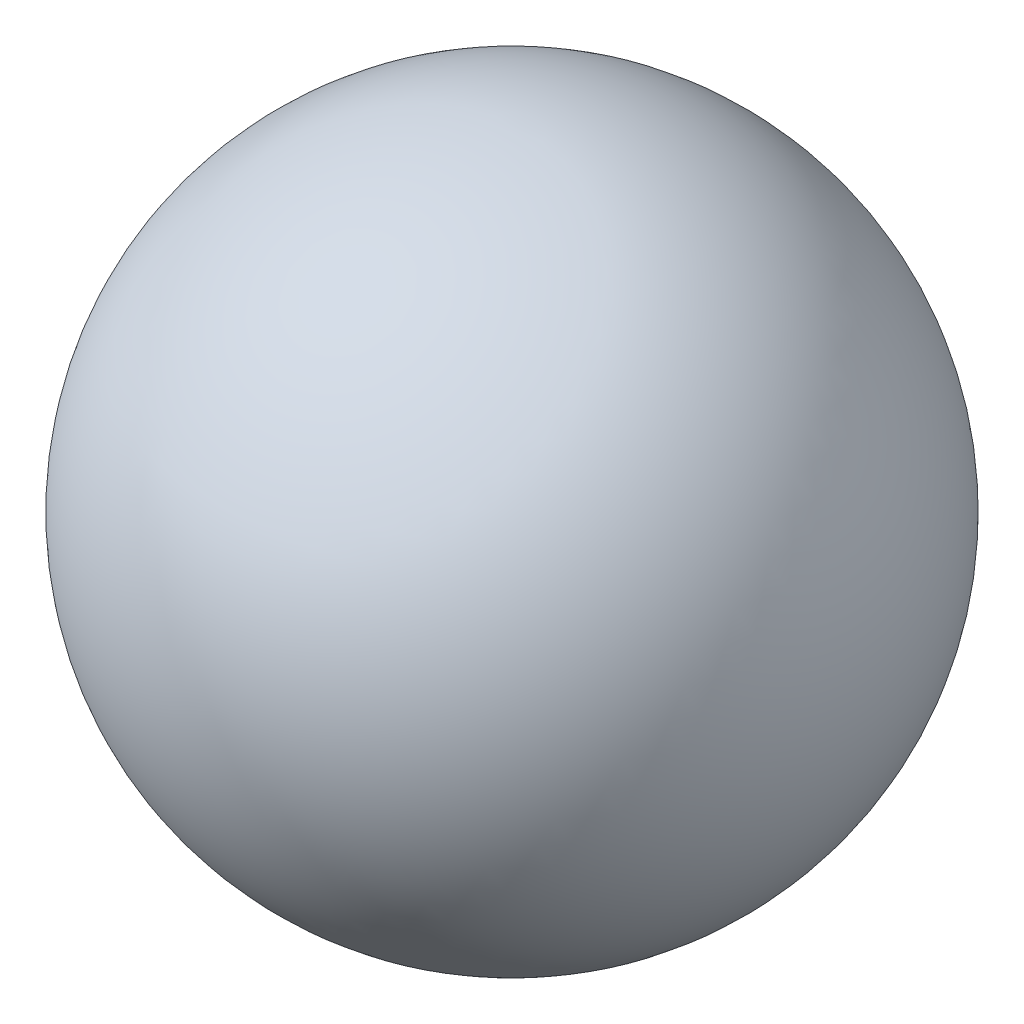
SolidWorks part; units mm, degrees
ref_plane "Front Plane" through (0, 0, 0) normal (0, 0, 1) x (1, 0, 0)
ref_plane "Top Plane" through (0, 0, 0) normal (0, 1, 0) x (1, 0, 0)
ref_plane "Right Plane" through (0, 0, 0) normal (1, 0, 0) x (0, 0, -1)
sketch "Sketch1" plane through (0, 0, 0) normal (1, 0, 0) x (0, 0, -1)
  line L0 (0, 0) -> (0, -21.5) construction
  line L1 (0, 21.5) -> (0, -21.5)
  arc A0 (0, -21.5) -> (0, 21.5) centre (0, 0) cw
revolve "Revolve4" add sketch "Sketch1" angle 360 about L0
